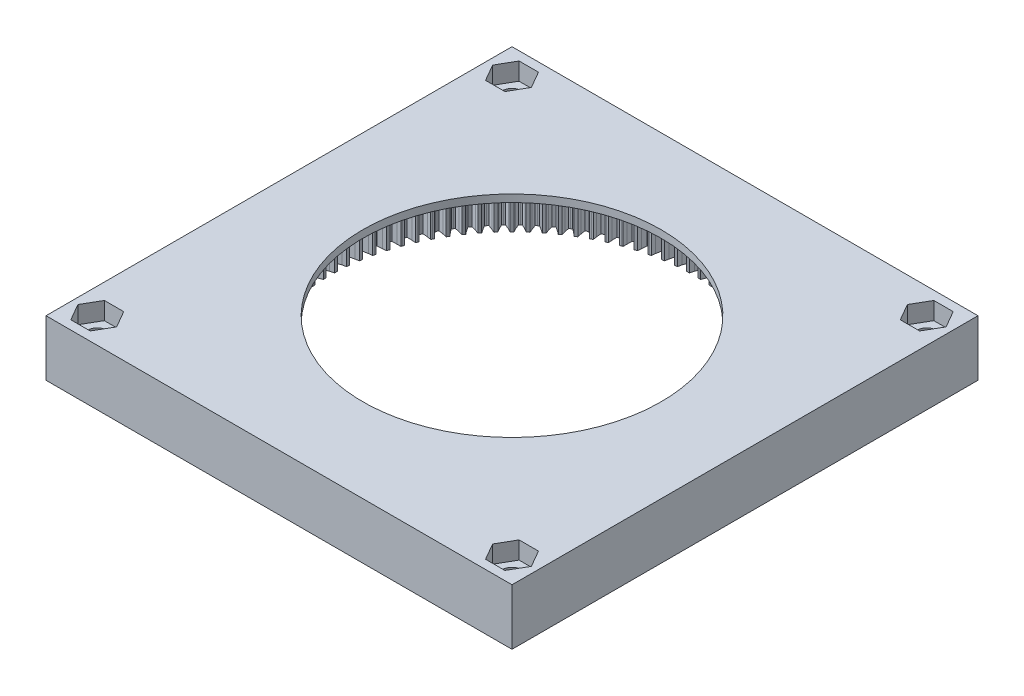
SolidWorks part; units mm, degrees
ref_plane "Front Plane" through (0, 0, 0) normal (0, 0, 1) x (1, 0, 0)
ref_plane "Top Plane" through (0, 0, 0) normal (0, 1, 0) x (1, 0, 0)
ref_plane "Right Plane" through (0, 0, 0) normal (1, 0, 0) x (0, 0, -1)
sketch "Sketch1" plane through (0, 0, 0) normal (0, 1, 0) x (1, 0, 0)
  line L1 (-79.375, -79.375) -> (79.375, -79.375)
  line L2 (-79.375, -79.375) -> (-79.375, 79.375)
  line L3 (-79.375, 79.375) -> (79.375, 79.375)
  line L4 (79.375, -79.375) -> (79.375, 79.375)
  line L5 (-79.375, -79.375) -> (79.375, 79.375) construction
  line L6 (-79.375, 79.375) -> (79.375, -79.375) construction
  dimension "D2" = 158.75
extrude "Boss-Extrude1" add sketch "Sketch1" along normal blind 19.05
sketch "Sketch7" plane through (0, 0, 0) normal (0, 1, 0) x (1, 0, 0)
  line L1 (-70.6438, -70.6438) -> (70.6437, -70.6438) construction
  line L2 (-70.6438, -70.6438) -> (-70.6438, 70.6437) construction
  line L3 (-70.6438, 70.6437) -> (70.6437, 70.6437) construction
  line L4 (70.6437, -70.6438) -> (70.6437, 70.6437) construction
  line L5 (-70.6438, -70.6438) -> (70.6437, 70.6437) construction
  line L6 (-70.6438, 70.6437) -> (70.6437, -70.6438) construction
  circle A0 centre (-70.6438, 70.6437) radius 3.3731
  circle A1 centre (70.6437, 70.6437) radius 3.3731
  circle A2 centre (70.6437, -70.6438) radius 3.3731
  circle A3 centre (-70.6438, -70.6438) radius 3.3731
  point P0 (0, 0)
  dimension "D2" = 6.7462
  dimension "D1" = 141.2875
extrude "Cut-Extrude2" cut sketch "Sketch7" along normal up to surface (19.05 mm away) up to face at (0, 19.05, 0)
sketch "Sketch8" plane through (0, 0, 0) normal (0, 1, 0) x (1, 0, 0)
  circle A0 centre (0, 0) radius 50.8
  dimension "D1" = 101.6
extrude "Cut-Extrude3" cut sketch "Sketch8" along normal up to surface (19.05 mm away) up to face at (-70.6438, 19.05, 67.2706)
sketch "Sketch10" plane through (0, 0, 0) normal (0, -1, 0) x (1, 0, 0)
  line L0 (61.8949, -1.477) -> (63.199, -1.0966)
  line L1 (63.199, -1.0966) -> (64.768, -0.5126)
  line L2 (64.768, -0.5126) -> (64.77, 0)
  line L3 (64.77, 0) -> (64.768, 0.5126)
  line L4 (64.768, 0.5126) -> (63.199, 1.0966)
  line L5 (63.199, 1.0966) -> (61.8949, 1.477)
  line L6 (61.8949, 1.477) -> (61.8819, 1.9447)
  line L7 (61.8819, 1.9447) -> (61.8655, 2.4123)
  line L8 (61.8655, 2.4123) -> (63.1432, 2.8739)
  line L9 (63.1432, 2.8739) -> (64.6724, 3.5553)
  line L10 (64.6724, 3.5553) -> (64.6422, 4.0669)
  line L11 (64.6422, 4.0669) -> (64.608, 4.5784)
  line L12 (64.608, 4.5784) -> (63.0054, 5.0627)
  line L13 (63.0054, 5.0627) -> (61.68, 5.3605)
  line L14 (61.68, 5.3605) -> (61.6377, 5.8265)
  line L15 (61.6377, 5.8265) -> (61.5919, 6.2921)
  line L16 (61.5919, 6.2921) -> (62.8381, 6.833)
  line L17 (62.8381, 6.833) -> (64.3215, 7.6091)
  line L18 (64.3215, 7.6091) -> (64.2593, 8.1178)
  line L19 (64.2593, 8.1178) -> (64.193, 8.6261)
  line L20 (64.193, 8.6261) -> (62.5632, 9.0089)
  line L21 (62.5632, 9.0089) -> (61.2217, 9.2229)
  line L22 (61.2217, 9.2229) -> (61.1503, 9.6852)
  line L23 (61.1503, 9.6852) -> (61.0753, 10.1471)
  line L24 (61.0753, 10.1471) -> (62.2851, 10.7652)
  line L25 (62.2851, 10.7652) -> (63.7168, 11.6328)
  line L26 (63.7168, 11.6328) -> (63.6227, 12.1367)
  line L27 (63.6227, 12.1367) -> (63.5247, 12.6398)
  line L28 (63.5247, 12.6398) -> (61.8741, 12.9195)
  line L29 (61.8741, 12.9195) -> (60.5218, 13.0488)
  line L30 (60.5218, 13.0488) -> (60.4214, 13.5058)
  line L31 (60.4214, 13.5058) -> (60.3177, 13.962)
  line L32 (60.3177, 13.962) -> (61.4862, 14.6548)
  line L33 (61.4862, 14.6548) -> (62.8606, 15.6107)
  line L34 (62.8606, 15.6107) -> (62.7351, 16.1076)
  line L35 (62.7351, 16.1076) -> (62.6057, 16.6036)
  line L36 (62.6057, 16.6036) -> (60.9408, 16.7791)
  line L37 (60.9408, 16.7791) -> (59.583, 16.8233)
  line L38 (59.583, 16.8233) -> (59.4542, 17.273)
  line L39 (59.4542, 17.273) -> (59.322, 17.7218)
  line L40 (59.322, 17.7218) -> (60.4447, 18.4867)
  line L41 (60.4447, 18.4867) -> (61.7564, 19.5269)
  line L42 (61.7564, 19.5269) -> (61.5999, 20.015)
  line L43 (61.5999, 20.015) -> (61.4396, 20.5019)
  line L44 (61.4396, 20.5019) -> (59.767, 20.5725)
  line L45 (59.767, 20.5725) -> (58.4091, 20.5313)
  line L46 (58.4091, 20.5313) -> (58.2523, 20.9721)
  line L47 (58.2523, 20.9721) -> (58.0921, 21.4117)
  line L48 (58.0921, 21.4117) -> (59.1646, 22.2455)
  line L49 (59.1646, 22.2455) -> (60.4084, 23.3661)
  line L50 (60.4084, 23.3661) -> (60.2216, 23.8434)
  line L51 (60.2216, 23.8434) -> (60.031, 24.3193)
  line L52 (60.031, 24.3193) -> (58.3573, 24.2847)
  line L53 (58.3573, 24.2847) -> (57.0047, 24.1583)
  line L54 (57.0047, 24.1583) -> (56.8205, 24.5884)
  line L55 (56.8205, 24.5884) -> (56.633, 25.0171)
  line L56 (56.633, 25.0171) -> (57.6511, 25.9166)
  line L57 (57.6511, 25.9166) -> (58.8221, 27.1131)
  line L58 (58.8221, 27.1131) -> (58.6056, 27.5777)
  line L59 (58.6056, 27.5777) -> (58.3856, 28.0406)
  line L60 (58.3856, 28.0406) -> (56.7173, 27.901)
  line L61 (56.7173, 27.901) -> (55.3753, 27.69)
  line L62 (55.3753, 27.69) -> (55.1644, 28.1077)
  line L63 (55.1644, 28.1077) -> (54.9505, 28.5238)
  line L64 (54.9505, 28.5238) -> (55.91, 29.4854)
  line L65 (55.91, 29.4854) -> (57.0035, 30.753)
  line L66 (57.0035, 30.753) -> (56.7584, 31.2032)
  line L67 (56.7584, 31.2032) -> (56.5097, 31.6514)
  line L68 (56.5097, 31.6514) -> (54.8534, 31.4073)
  line L69 (54.8534, 31.4073) -> (53.5273, 31.1124)
  line L70 (53.5273, 31.1124) -> (53.2907, 31.516)
  line L71 (53.2907, 31.516) -> (53.051, 31.9178)
  line L72 (53.051, 31.9178) -> (53.9483, 32.9379)
  line L73 (53.9483, 32.9379) -> (54.9601, 34.2716)
  line L74 (54.9601, 34.2716) -> (54.6871, 34.7055)
  line L75 (54.6871, 34.7055) -> (54.4108, 35.1372)
  line L76 (54.4108, 35.1372) -> (52.7731, 34.7896)
  line L77 (52.7731, 34.7896) -> (51.4681, 34.412)
  line L78 (51.4681, 34.412) -> (51.2066, 34.8)
  line L79 (51.2066, 34.8) -> (50.9422, 35.186)
  line L80 (50.9422, 35.186) -> (51.7736, 36.2603)
  line L81 (51.7736, 36.2603) -> (52.6997, 37.655)
  line L82 (52.6997, 37.655) -> (52.4, 38.0709)
  line L83 (52.4, 38.0709) -> (52.0971, 38.4843)
  line L84 (52.0971, 38.4843) -> (50.4845, 38.0346)
  line L85 (50.4845, 38.0346) -> (49.2058, 37.5758)
  line L86 (49.2058, 37.5758) -> (48.9205, 37.9466)
  line L87 (48.9205, 37.9466) -> (48.6323, 38.3152)
  line L88 (48.6323, 38.3152) -> (49.3946, 39.4396)
  line L89 (49.3946, 39.4396) -> (50.2313, 40.8897)
  line L90 (50.2313, 40.8897) -> (49.9061, 41.286)
  line L91 (49.9061, 41.286) -> (49.5779, 41.6796)
  line L92 (49.5779, 41.6796) -> (47.9967, 41.1295)
  line L93 (47.9967, 41.1295) -> (46.7493, 40.5913)
  line L94 (46.7493, 40.5913) -> (46.4413, 40.9435)
  line L95 (46.4413, 40.9435) -> (46.1305, 41.2933)
  line L96 (46.1305, 41.2933) -> (46.8207, 42.4633)
  line L97 (46.8207, 42.4633) -> (47.5647, 43.9631)
  line L98 (47.5647, 43.9631) -> (47.2153, 44.3381)
  line L99 (47.2153, 44.3381) -> (46.8629, 44.7104)
  line L100 (46.8629, 44.7104) -> (45.3194, 44.0621)
  line L101 (45.3194, 44.0621) -> (44.1083, 43.4467)
  line L102 (44.1083, 43.4467) -> (43.7787, 43.7787)
  line L103 (43.7787, 43.7787) -> (43.4467, 44.1083)
  line L104 (43.4467, 44.1083) -> (44.0621, 45.3194)
  line L105 (44.0621, 45.3194) -> (44.7104, 46.8629)
  line L106 (44.7104, 46.8629) -> (44.3381, 47.2153)
  line L107 (44.3381, 47.2153) -> (43.9631, 47.5647)
  line L108 (43.9631, 47.5647) -> (42.4633, 46.8207)
  line L109 (42.4633, 46.8207) -> (41.2933, 46.1305)
  line L110 (41.2933, 46.1305) -> (40.9435, 46.4413)
  line L111 (40.9435, 46.4413) -> (40.5913, 46.7493)
  line L112 (40.5913, 46.7493) -> (41.1295, 47.9967)
  line L113 (41.1295, 47.9967) -> (41.6796, 49.5779)
  line L114 (41.6796, 49.5779) -> (41.286, 49.9061)
  line L115 (41.286, 49.9061) -> (40.8897, 50.2313)
  line L116 (40.8897, 50.2313) -> (39.4396, 49.3946)
  line L117 (39.4396, 49.3946) -> (38.3152, 48.6323)
  line L118 (38.3152, 48.6323) -> (37.9466, 48.9205)
  line L119 (37.9466, 48.9205) -> (37.5758, 49.2058)
  line L120 (37.5758, 49.2058) -> (38.0346, 50.4845)
  line L121 (38.0346, 50.4845) -> (38.4843, 52.0971)
  line L122 (38.4843, 52.0971) -> (38.0709, 52.4)
  line L123 (38.0709, 52.4) -> (37.655, 52.6997)
  line L124 (37.655, 52.6997) -> (36.2603, 51.7736)
  line L125 (36.2603, 51.7736) -> (35.186, 50.9422)
  line L126 (35.186, 50.9422) -> (34.8, 51.2066)
  line L127 (34.8, 51.2066) -> (34.412, 51.4681)
  line L128 (34.412, 51.4681) -> (34.7896, 52.7731)
  line L129 (34.7896, 52.7731) -> (35.1372, 54.4108)
  line L130 (35.1372, 54.4108) -> (34.7055, 54.6871)
  line L131 (34.7055, 54.6871) -> (34.2716, 54.9601)
  line L132 (34.2716, 54.9601) -> (32.9379, 53.9483)
  line L133 (32.9379, 53.9483) -> (31.9178, 53.051)
  line L134 (31.9178, 53.051) -> (31.516, 53.2907)
  line L135 (31.516, 53.2907) -> (31.1124, 53.5273)
  line L136 (31.1124, 53.5273) -> (31.4073, 54.8534)
  line L137 (31.4073, 54.8534) -> (31.6514, 56.5097)
  line L138 (31.6514, 56.5097) -> (31.2032, 56.7584)
  line L139 (31.2032, 56.7584) -> (30.753, 57.0035)
  line L140 (30.753, 57.0035) -> (29.4854, 55.91)
  line L141 (29.4854, 55.91) -> (28.5238, 54.9505)
  line L142 (28.5238, 54.9505) -> (28.1077, 55.1644)
  line L143 (28.1077, 55.1644) -> (27.69, 55.3753)
  line L144 (27.69, 55.3753) -> (27.901, 56.7173)
  line L145 (27.901, 56.7173) -> (28.0406, 58.3856)
  line L146 (28.0406, 58.3856) -> (27.5777, 58.6056)
  line L147 (27.5777, 58.6056) -> (27.1131, 58.8221)
  line L148 (27.1131, 58.8221) -> (25.9166, 57.6511)
  line L149 (25.9166, 57.6511) -> (25.0171, 56.633)
  line L150 (25.0171, 56.633) -> (24.5884, 56.8205)
  line L151 (24.5884, 56.8205) -> (24.1583, 57.0047)
  line L152 (24.1583, 57.0047) -> (24.2847, 58.3573)
  line L153 (24.2847, 58.3573) -> (24.3193, 60.031)
  line L154 (24.3193, 60.031) -> (23.8434, 60.2216)
  line L155 (23.8434, 60.2216) -> (23.3661, 60.4084)
  line L156 (23.3661, 60.4084) -> (22.2455, 59.1646)
  line L157 (22.2455, 59.1646) -> (21.4117, 58.0921)
  line L158 (21.4117, 58.0921) -> (20.9721, 58.2523)
  line L159 (20.9721, 58.2523) -> (20.5313, 58.4091)
  line L160 (20.5313, 58.4091) -> (20.5725, 59.767)
  line L161 (20.5725, 59.767) -> (20.5019, 61.4396)
  line L162 (20.5019, 61.4396) -> (20.015, 61.5999)
  line L163 (20.015, 61.5999) -> (19.5269, 61.7564)
  line L164 (19.5269, 61.7564) -> (18.4867, 60.4447)
  line L165 (18.4867, 60.4447) -> (17.7218, 59.322)
  line L166 (17.7218, 59.322) -> (17.273, 59.4542)
  line L167 (17.273, 59.4542) -> (16.8233, 59.583)
  line L168 (16.8233, 59.583) -> (16.7791, 60.9408)
  line L169 (16.7791, 60.9408) -> (16.6036, 62.6057)
  line L170 (16.6036, 62.6057) -> (16.1076, 62.7351)
  line L171 (16.1076, 62.7351) -> (15.6107, 62.8606)
  line L172 (15.6107, 62.8606) -> (14.6548, 61.4862)
  line L173 (14.6548, 61.4862) -> (13.962, 60.3177)
  line L174 (13.962, 60.3177) -> (13.5058, 60.4214)
  line L175 (13.5058, 60.4214) -> (13.0488, 60.5218)
  line L176 (13.0488, 60.5218) -> (12.9195, 61.8741)
  line L177 (12.9195, 61.8741) -> (12.6398, 63.5247)
  line L178 (12.6398, 63.5247) -> (12.1367, 63.6227)
  line L179 (12.1367, 63.6227) -> (11.6328, 63.7168)
  line L180 (11.6328, 63.7168) -> (10.7652, 62.2851)
  line L181 (10.7652, 62.2851) -> (10.1471, 61.0753)
  line L182 (10.1471, 61.0753) -> (9.6852, 61.1503)
  line L183 (9.6852, 61.1503) -> (9.2229, 61.2217)
  line L184 (9.2229, 61.2217) -> (9.0089, 62.5632)
  line L185 (9.0089, 62.5632) -> (8.6261, 64.193)
  line L186 (8.6261, 64.193) -> (8.1178, 64.2593)
  line L187 (8.1178, 64.2593) -> (7.6091, 64.3215)
  line L188 (7.6091, 64.3215) -> (6.833, 62.8381)
  line L189 (6.833, 62.8381) -> (6.2921, 61.5919)
  line L190 (6.2921, 61.5919) -> (5.8265, 61.6377)
  line L191 (5.8265, 61.6377) -> (5.3605, 61.68)
  line L192 (5.3605, 61.68) -> (5.0627, 63.0054)
  line L193 (5.0627, 63.0054) -> (4.5784, 64.608)
  line L194 (4.5784, 64.608) -> (4.0669, 64.6422)
  line L195 (4.0669, 64.6422) -> (3.5553, 64.6724)
  line L196 (3.5553, 64.6724) -> (2.8739, 63.1432)
  line L197 (2.8739, 63.1432) -> (2.4123, 61.8655)
  line L198 (2.4123, 61.8655) -> (1.9447, 61.8819)
  line L199 (1.9447, 61.8819) -> (1.477, 61.8949)
  line L200 (1.477, 61.8949) -> (1.0966, 63.199)
  line L201 (1.0966, 63.199) -> (0.5126, 64.768)
  line L202 (0.5126, 64.768) -> (0, 64.77)
  line L203 (0, 64.77) -> (-0.5126, 64.768)
  line L204 (-0.5126, 64.768) -> (-1.0966, 63.199)
  line L205 (-1.0966, 63.199) -> (-1.477, 61.8949)
  line L206 (-1.477, 61.8949) -> (-1.9447, 61.8819)
  line L207 (-1.9447, 61.8819) -> (-2.4123, 61.8655)
  line L208 (-2.4123, 61.8655) -> (-2.8739, 63.1432)
  line L209 (-2.8739, 63.1432) -> (-3.5553, 64.6724)
  line L210 (-3.5553, 64.6724) -> (-4.0669, 64.6422)
  line L211 (-4.0669, 64.6422) -> (-4.5784, 64.608)
  line L212 (-4.5784, 64.608) -> (-5.0627, 63.0054)
  line L213 (-5.0627, 63.0054) -> (-5.3605, 61.68)
  line L214 (-5.3605, 61.68) -> (-5.8265, 61.6377)
  line L215 (-5.8265, 61.6377) -> (-6.2921, 61.5919)
  line L216 (-6.2921, 61.5919) -> (-6.833, 62.8381)
  line L217 (-6.833, 62.8381) -> (-7.6091, 64.3215)
  line L218 (-7.6091, 64.3215) -> (-8.1178, 64.2593)
  line L219 (-8.1178, 64.2593) -> (-8.6261, 64.193)
  line L220 (-8.6261, 64.193) -> (-9.0089, 62.5632)
  line L221 (-9.0089, 62.5632) -> (-9.2229, 61.2217)
  line L222 (-9.2229, 61.2217) -> (-9.6852, 61.1503)
  line L223 (-9.6852, 61.1503) -> (-10.1471, 61.0753)
  line L224 (-10.1471, 61.0753) -> (-10.7652, 62.2851)
  line L225 (-10.7652, 62.2851) -> (-11.6328, 63.7168)
  line L226 (-11.6328, 63.7168) -> (-12.1367, 63.6227)
  line L227 (-12.1367, 63.6227) -> (-12.6398, 63.5247)
  line L228 (-12.6398, 63.5247) -> (-12.9195, 61.8741)
  line L229 (-12.9195, 61.8741) -> (-13.0488, 60.5218)
  line L230 (-13.0488, 60.5218) -> (-13.5058, 60.4214)
  line L231 (-13.5058, 60.4214) -> (-13.962, 60.3177)
  line L232 (-13.962, 60.3177) -> (-14.6548, 61.4862)
  line L233 (-14.6548, 61.4862) -> (-15.6107, 62.8606)
  line L234 (-15.6107, 62.8606) -> (-16.1076, 62.7351)
  line L235 (-16.1076, 62.7351) -> (-16.6036, 62.6057)
  line L236 (-16.6036, 62.6057) -> (-16.7791, 60.9408)
  line L237 (-16.7791, 60.9408) -> (-16.8233, 59.583)
  line L238 (-16.8233, 59.583) -> (-17.273, 59.4542)
  line L239 (-17.273, 59.4542) -> (-17.7218, 59.322)
  line L240 (-17.7218, 59.322) -> (-18.4867, 60.4447)
  line L241 (-18.4867, 60.4447) -> (-19.5269, 61.7564)
  line L242 (-19.5269, 61.7564) -> (-20.015, 61.5999)
  line L243 (-20.015, 61.5999) -> (-20.5019, 61.4396)
  line L244 (-20.5019, 61.4396) -> (-20.5725, 59.767)
  line L245 (-20.5725, 59.767) -> (-20.5313, 58.4091)
  line L246 (-20.5313, 58.4091) -> (-20.9721, 58.2523)
  line L247 (-20.9721, 58.2523) -> (-21.4117, 58.0921)
  line L248 (-21.4117, 58.0921) -> (-22.2455, 59.1646)
  line L249 (-22.2455, 59.1646) -> (-23.3661, 60.4084)
  line L250 (-23.3661, 60.4084) -> (-23.8434, 60.2216)
  line L251 (-23.8434, 60.2216) -> (-24.3193, 60.031)
  line L252 (-24.3193, 60.031) -> (-24.2847, 58.3573)
  line L253 (-24.2847, 58.3573) -> (-24.1583, 57.0047)
  line L254 (-24.1583, 57.0047) -> (-24.5884, 56.8205)
  line L255 (-24.5884, 56.8205) -> (-25.0171, 56.633)
  line L256 (-25.0171, 56.633) -> (-25.9166, 57.6511)
  line L257 (-25.9166, 57.6511) -> (-27.1131, 58.8221)
  line L258 (-27.1131, 58.8221) -> (-27.5777, 58.6056)
  line L259 (-27.5777, 58.6056) -> (-28.0406, 58.3856)
  line L260 (-28.0406, 58.3856) -> (-27.901, 56.7173)
  line L261 (-27.901, 56.7173) -> (-27.69, 55.3753)
  line L262 (-27.69, 55.3753) -> (-28.1077, 55.1644)
  line L263 (-28.1077, 55.1644) -> (-28.5238, 54.9505)
  line L264 (-28.5238, 54.9505) -> (-29.4854, 55.91)
  line L265 (-29.4854, 55.91) -> (-30.753, 57.0035)
  line L266 (-30.753, 57.0035) -> (-31.2032, 56.7584)
  line L267 (-31.2032, 56.7584) -> (-31.6514, 56.5097)
  line L268 (-31.6514, 56.5097) -> (-31.4073, 54.8534)
  line L269 (-31.4073, 54.8534) -> (-31.1124, 53.5273)
  line L270 (-31.1124, 53.5273) -> (-31.516, 53.2907)
  line L271 (-31.516, 53.2907) -> (-31.9178, 53.051)
  line L272 (-31.9178, 53.051) -> (-32.9379, 53.9483)
  line L273 (-32.9379, 53.9483) -> (-34.2716, 54.9601)
  line L274 (-34.2716, 54.9601) -> (-34.7055, 54.6871)
  line L275 (-34.7055, 54.6871) -> (-35.1372, 54.4108)
  line L276 (-35.1372, 54.4108) -> (-34.7896, 52.7731)
  line L277 (-34.7896, 52.7731) -> (-34.412, 51.4681)
  line L278 (-34.412, 51.4681) -> (-34.8, 51.2066)
  line L279 (-34.8, 51.2066) -> (-35.186, 50.9422)
  line L280 (-35.186, 50.9422) -> (-36.2603, 51.7736)
  line L281 (-36.2603, 51.7736) -> (-37.655, 52.6997)
  line L282 (-37.655, 52.6997) -> (-38.0709, 52.4)
  line L283 (-38.0709, 52.4) -> (-38.4843, 52.0971)
  line L284 (-38.4843, 52.0971) -> (-38.0346, 50.4845)
  line L285 (-38.0346, 50.4845) -> (-37.5758, 49.2058)
  line L286 (-37.5758, 49.2058) -> (-37.9466, 48.9205)
  line L287 (-37.9466, 48.9205) -> (-38.3152, 48.6323)
  line L288 (-38.3152, 48.6323) -> (-39.4396, 49.3946)
  line L289 (-39.4396, 49.3946) -> (-40.8897, 50.2313)
  line L290 (-40.8897, 50.2313) -> (-41.286, 49.9061)
  line L291 (-41.286, 49.9061) -> (-41.6796, 49.5779)
  line L292 (-41.6796, 49.5779) -> (-41.1295, 47.9967)
  line L293 (-41.1295, 47.9967) -> (-40.5913, 46.7493)
  line L294 (-40.5913, 46.7493) -> (-40.9435, 46.4413)
  line L295 (-40.9435, 46.4413) -> (-41.2933, 46.1305)
  line L296 (-41.2933, 46.1305) -> (-42.4633, 46.8207)
  line L297 (-42.4633, 46.8207) -> (-43.9631, 47.5647)
  line L298 (-43.9631, 47.5647) -> (-44.3381, 47.2153)
  line L299 (-44.3381, 47.2153) -> (-44.7104, 46.8629)
  line L300 (-44.7104, 46.8629) -> (-44.0621, 45.3194)
  line L301 (-44.0621, 45.3194) -> (-43.4467, 44.1083)
  line L302 (-43.4467, 44.1083) -> (-43.7787, 43.7787)
  line L303 (-43.7787, 43.7787) -> (-44.1083, 43.4467)
  line L304 (-44.1083, 43.4467) -> (-45.3194, 44.0621)
  line L305 (-45.3194, 44.0621) -> (-46.8629, 44.7104)
  line L306 (-46.8629, 44.7104) -> (-47.2153, 44.3381)
  line L307 (-47.2153, 44.3381) -> (-47.5647, 43.9631)
  line L308 (-47.5647, 43.9631) -> (-46.8207, 42.4633)
  line L309 (-46.8207, 42.4633) -> (-46.1305, 41.2933)
  line L310 (-46.1305, 41.2933) -> (-46.4413, 40.9435)
  line L311 (-46.4413, 40.9435) -> (-46.7493, 40.5913)
  line L312 (-46.7493, 40.5913) -> (-47.9967, 41.1295)
  line L313 (-47.9967, 41.1295) -> (-49.5779, 41.6796)
  line L314 (-49.5779, 41.6796) -> (-49.9061, 41.286)
  line L315 (-49.9061, 41.286) -> (-50.2313, 40.8897)
  line L316 (-50.2313, 40.8897) -> (-49.3946, 39.4396)
  line L317 (-49.3946, 39.4396) -> (-48.6323, 38.3152)
  line L318 (-48.6323, 38.3152) -> (-48.9205, 37.9466)
  line L319 (-48.9205, 37.9466) -> (-49.2058, 37.5758)
  line L320 (-49.2058, 37.5758) -> (-50.4845, 38.0346)
  line L321 (-50.4845, 38.0346) -> (-52.0971, 38.4843)
  line L322 (-52.0971, 38.4843) -> (-52.4, 38.0709)
  line L323 (-52.4, 38.0709) -> (-52.6997, 37.655)
  line L324 (-52.6997, 37.655) -> (-51.7736, 36.2603)
  line L325 (-51.7736, 36.2603) -> (-50.9422, 35.186)
  line L326 (-50.9422, 35.186) -> (-51.2066, 34.8)
  line L327 (-51.2066, 34.8) -> (-51.4681, 34.412)
  line L328 (-51.4681, 34.412) -> (-52.7731, 34.7896)
  line L329 (-52.7731, 34.7896) -> (-54.4108, 35.1372)
  line L330 (-54.4108, 35.1372) -> (-54.6871, 34.7055)
  line L331 (-54.6871, 34.7055) -> (-54.9601, 34.2716)
  line L332 (-54.9601, 34.2716) -> (-53.9483, 32.9379)
  line L333 (-53.9483, 32.9379) -> (-53.051, 31.9178)
  line L334 (-53.051, 31.9178) -> (-53.2907, 31.516)
  line L335 (-53.2907, 31.516) -> (-53.5273, 31.1124)
  line L336 (-53.5273, 31.1124) -> (-54.8534, 31.4073)
  line L337 (-54.8534, 31.4073) -> (-56.5097, 31.6514)
  line L338 (-56.5097, 31.6514) -> (-56.7584, 31.2032)
  line L339 (-56.7584, 31.2032) -> (-57.0035, 30.753)
  line L340 (-57.0035, 30.753) -> (-55.91, 29.4854)
  line L341 (-55.91, 29.4854) -> (-54.9505, 28.5238)
  line L342 (-54.9505, 28.5238) -> (-55.1644, 28.1077)
  line L343 (-55.1644, 28.1077) -> (-55.3753, 27.69)
  line L344 (-55.3753, 27.69) -> (-56.7173, 27.901)
  line L345 (-56.7173, 27.901) -> (-58.3856, 28.0406)
  line L346 (-58.3856, 28.0406) -> (-58.6056, 27.5777)
  line L347 (-58.6056, 27.5777) -> (-58.8221, 27.1131)
  line L348 (-58.8221, 27.1131) -> (-57.6511, 25.9166)
  line L349 (-57.6511, 25.9166) -> (-56.633, 25.0171)
  line L350 (-56.633, 25.0171) -> (-56.8205, 24.5884)
  line L351 (-56.8205, 24.5884) -> (-57.0047, 24.1583)
  line L352 (-57.0047, 24.1583) -> (-58.3573, 24.2847)
  line L353 (-58.3573, 24.2847) -> (-60.031, 24.3193)
  line L354 (-60.031, 24.3193) -> (-60.2216, 23.8434)
  line L355 (-60.2216, 23.8434) -> (-60.4084, 23.3661)
  line L356 (-60.4084, 23.3661) -> (-59.1646, 22.2455)
  line L357 (-59.1646, 22.2455) -> (-58.0921, 21.4117)
  line L358 (-58.0921, 21.4117) -> (-58.2523, 20.9721)
  line L359 (-58.2523, 20.9721) -> (-58.4091, 20.5313)
  line L360 (-58.4091, 20.5313) -> (-59.767, 20.5725)
  line L361 (-59.767, 20.5725) -> (-61.4396, 20.5019)
  line L362 (-61.4396, 20.5019) -> (-61.5999, 20.015)
  line L363 (-61.5999, 20.015) -> (-61.7564, 19.5269)
  line L364 (-61.7564, 19.5269) -> (-60.4447, 18.4867)
  line L365 (-60.4447, 18.4867) -> (-59.322, 17.7218)
  line L366 (-59.322, 17.7218) -> (-59.4542, 17.273)
  line L367 (-59.4542, 17.273) -> (-59.583, 16.8233)
  line L368 (-59.583, 16.8233) -> (-60.9408, 16.7791)
  line L369 (-60.9408, 16.7791) -> (-62.6057, 16.6036)
  line L370 (-62.6057, 16.6036) -> (-62.7351, 16.1076)
  line L371 (-62.7351, 16.1076) -> (-62.8606, 15.6107)
  line L372 (-62.8606, 15.6107) -> (-61.4862, 14.6548)
  line L373 (-61.4862, 14.6548) -> (-60.3177, 13.962)
  line L374 (-60.3177, 13.962) -> (-60.4214, 13.5058)
  line L375 (-60.4214, 13.5058) -> (-60.5218, 13.0488)
  line L376 (-60.5218, 13.0488) -> (-61.8741, 12.9195)
  line L377 (-61.8741, 12.9195) -> (-63.5247, 12.6398)
  line L378 (-63.5247, 12.6398) -> (-63.6227, 12.1367)
  line L379 (-63.6227, 12.1367) -> (-63.7168, 11.6328)
  line L380 (-63.7168, 11.6328) -> (-62.2851, 10.7652)
  line L381 (-62.2851, 10.7652) -> (-61.0753, 10.1471)
  line L382 (-61.0753, 10.1471) -> (-61.1503, 9.6852)
  line L383 (-61.1503, 9.6852) -> (-61.2217, 9.2229)
  line L384 (-61.2217, 9.2229) -> (-62.5632, 9.0089)
  line L385 (-62.5632, 9.0089) -> (-64.193, 8.6261)
  line L386 (-64.193, 8.6261) -> (-64.2593, 8.1178)
  line L387 (-64.2593, 8.1178) -> (-64.3215, 7.6091)
  line L388 (-64.3215, 7.6091) -> (-62.8381, 6.833)
  line L389 (-62.8381, 6.833) -> (-61.5919, 6.2921)
  line L390 (-61.5919, 6.2921) -> (-61.6377, 5.8265)
  line L391 (-61.6377, 5.8265) -> (-61.68, 5.3605)
  line L392 (-61.68, 5.3605) -> (-63.0054, 5.0627)
  line L393 (-63.0054, 5.0627) -> (-64.608, 4.5784)
  line L394 (-64.608, 4.5784) -> (-64.6422, 4.0669)
  line L395 (-64.6422, 4.0669) -> (-64.6724, 3.5553)
  line L396 (-64.6724, 3.5553) -> (-63.1432, 2.8739)
  line L397 (-63.1432, 2.8739) -> (-61.8655, 2.4123)
  line L398 (-61.8655, 2.4123) -> (-61.8819, 1.9447)
  line L399 (-61.8819, 1.9447) -> (-61.8949, 1.477)
  line L400 (-61.8949, 1.477) -> (-63.199, 1.0966)
  line L401 (-63.199, 1.0966) -> (-64.768, 0.5126)
  line L402 (-64.768, 0.5126) -> (-64.77, 0)
  line L403 (-64.77, 0) -> (-64.768, -0.5126)
  line L404 (-64.768, -0.5126) -> (-63.199, -1.0966)
  line L405 (-63.199, -1.0966) -> (-61.8949, -1.477)
  line L406 (-61.8949, -1.477) -> (-61.8819, -1.9447)
  line L407 (-61.8819, -1.9447) -> (-61.8655, -2.4123)
  line L408 (-61.8655, -2.4123) -> (-63.1432, -2.8739)
  line L409 (-63.1432, -2.8739) -> (-64.6724, -3.5553)
  line L410 (-64.6724, -3.5553) -> (-64.6422, -4.0669)
  line L411 (-64.6422, -4.0669) -> (-64.608, -4.5784)
  line L412 (-64.608, -4.5784) -> (-63.0054, -5.0627)
  line L413 (-63.0054, -5.0627) -> (-61.68, -5.3605)
  line L414 (-61.68, -5.3605) -> (-61.6377, -5.8265)
  line L415 (-61.6377, -5.8265) -> (-61.5919, -6.2921)
  line L416 (-61.5919, -6.2921) -> (-62.8381, -6.833)
  line L417 (-62.8381, -6.833) -> (-64.3215, -7.6091)
  line L418 (-64.3215, -7.6091) -> (-64.2593, -8.1178)
  line L419 (-64.2593, -8.1178) -> (-64.193, -8.6261)
  line L420 (-64.193, -8.6261) -> (-62.5632, -9.0089)
  line L421 (-62.5632, -9.0089) -> (-61.2217, -9.2229)
  line L422 (-61.2217, -9.2229) -> (-61.1503, -9.6852)
  line L423 (-61.1503, -9.6852) -> (-61.0753, -10.1471)
  line L424 (-61.0753, -10.1471) -> (-62.2851, -10.7652)
  line L425 (-62.2851, -10.7652) -> (-63.7168, -11.6328)
  line L426 (-63.7168, -11.6328) -> (-63.6227, -12.1367)
  line L427 (-63.6227, -12.1367) -> (-63.5247, -12.6398)
  line L428 (-63.5247, -12.6398) -> (-61.8741, -12.9195)
  line L429 (-61.8741, -12.9195) -> (-60.5218, -13.0488)
  line L430 (-60.5218, -13.0488) -> (-60.4214, -13.5058)
  line L431 (-60.4214, -13.5058) -> (-60.3177, -13.962)
  line L432 (-60.3177, -13.962) -> (-61.4862, -14.6548)
  line L433 (-61.4862, -14.6548) -> (-62.8606, -15.6107)
  line L434 (-62.8606, -15.6107) -> (-62.7351, -16.1076)
  line L435 (-62.7351, -16.1076) -> (-62.6057, -16.6036)
  line L436 (-62.6057, -16.6036) -> (-60.9408, -16.7791)
  line L437 (-60.9408, -16.7791) -> (-59.583, -16.8233)
  line L438 (-59.583, -16.8233) -> (-59.4542, -17.273)
  line L439 (-59.4542, -17.273) -> (-59.322, -17.7218)
  line L440 (-59.322, -17.7218) -> (-60.4447, -18.4867)
  line L441 (-60.4447, -18.4867) -> (-61.7564, -19.5269)
  line L442 (-61.7564, -19.5269) -> (-61.5999, -20.015)
  line L443 (-61.5999, -20.015) -> (-61.4396, -20.5019)
  line L444 (-61.4396, -20.5019) -> (-59.767, -20.5725)
  line L445 (-59.767, -20.5725) -> (-58.4091, -20.5313)
  line L446 (-58.4091, -20.5313) -> (-58.2523, -20.9721)
  line L447 (-58.2523, -20.9721) -> (-58.0921, -21.4117)
  line L448 (-58.0921, -21.4117) -> (-59.1646, -22.2455)
  line L449 (-59.1646, -22.2455) -> (-60.4084, -23.3661)
  line L450 (-60.4084, -23.3661) -> (-60.2216, -23.8434)
  line L451 (-60.2216, -23.8434) -> (-60.031, -24.3193)
  line L452 (-60.031, -24.3193) -> (-58.3573, -24.2847)
  line L453 (-58.3573, -24.2847) -> (-57.0047, -24.1583)
  line L454 (-57.0047, -24.1583) -> (-56.8205, -24.5884)
  line L455 (-56.8205, -24.5884) -> (-56.633, -25.0171)
  line L456 (-56.633, -25.0171) -> (-57.6511, -25.9166)
  line L457 (-57.6511, -25.9166) -> (-58.8221, -27.1131)
  line L458 (-58.8221, -27.1131) -> (-58.6056, -27.5777)
  line L459 (-58.6056, -27.5777) -> (-58.3856, -28.0406)
  line L460 (-58.3856, -28.0406) -> (-56.7173, -27.901)
  line L461 (-56.7173, -27.901) -> (-55.3753, -27.69)
  line L462 (-55.3753, -27.69) -> (-55.1644, -28.1077)
  line L463 (-55.1644, -28.1077) -> (-54.9505, -28.5238)
  line L464 (-54.9505, -28.5238) -> (-55.91, -29.4854)
  line L465 (-55.91, -29.4854) -> (-57.0035, -30.753)
  line L466 (-57.0035, -30.753) -> (-56.7584, -31.2032)
  line L467 (-56.7584, -31.2032) -> (-56.5097, -31.6514)
  line L468 (-56.5097, -31.6514) -> (-54.8534, -31.4073)
  line L469 (-54.8534, -31.4073) -> (-53.5273, -31.1124)
  line L470 (-53.5273, -31.1124) -> (-53.2907, -31.516)
  line L471 (-53.2907, -31.516) -> (-53.051, -31.9178)
  line L472 (-53.051, -31.9178) -> (-53.9483, -32.9379)
  line L473 (-53.9483, -32.9379) -> (-54.9601, -34.2716)
  line L474 (-54.9601, -34.2716) -> (-54.6871, -34.7055)
  line L475 (-54.6871, -34.7055) -> (-54.4108, -35.1372)
  line L476 (-54.4108, -35.1372) -> (-52.7731, -34.7896)
  line L477 (-52.7731, -34.7896) -> (-51.4681, -34.412)
  line L478 (-51.4681, -34.412) -> (-51.2066, -34.8)
  line L479 (-51.2066, -34.8) -> (-50.9422, -35.186)
  line L480 (-50.9422, -35.186) -> (-51.7736, -36.2603)
  line L481 (-51.7736, -36.2603) -> (-52.6997, -37.655)
  line L482 (-52.6997, -37.655) -> (-52.4, -38.0709)
  line L483 (-52.4, -38.0709) -> (-52.0971, -38.4843)
  line L484 (-52.0971, -38.4843) -> (-50.4845, -38.0346)
  line L485 (-50.4845, -38.0346) -> (-49.2058, -37.5758)
  line L486 (-49.2058, -37.5758) -> (-48.9205, -37.9466)
  line L487 (-48.9205, -37.9466) -> (-48.6323, -38.3152)
  line L488 (-48.6323, -38.3152) -> (-49.3946, -39.4396)
  line L489 (-49.3946, -39.4396) -> (-50.2313, -40.8897)
  line L490 (-50.2313, -40.8897) -> (-49.9061, -41.286)
  line L491 (-49.9061, -41.286) -> (-49.5779, -41.6796)
  line L492 (-49.5779, -41.6796) -> (-47.9967, -41.1295)
  line L493 (-47.9967, -41.1295) -> (-46.7493, -40.5913)
  line L494 (-46.7493, -40.5913) -> (-46.4413, -40.9435)
  line L495 (-46.4413, -40.9435) -> (-46.1305, -41.2933)
  line L496 (-46.1305, -41.2933) -> (-46.8207, -42.4633)
  line L497 (-46.8207, -42.4633) -> (-47.5647, -43.9631)
  line L498 (-47.5647, -43.9631) -> (-47.2153, -44.3381)
  line L499 (-47.2153, -44.3381) -> (-46.8629, -44.7104)
  line L500 (-46.8629, -44.7104) -> (-45.3194, -44.0621)
  line L501 (-45.3194, -44.0621) -> (-44.1083, -43.4467)
  line L502 (-44.1083, -43.4467) -> (-43.7787, -43.7787)
  line L503 (-43.7787, -43.7787) -> (-43.4467, -44.1083)
  line L504 (-43.4467, -44.1083) -> (-44.0621, -45.3194)
  line L505 (-44.0621, -45.3194) -> (-44.7104, -46.8629)
  line L506 (-44.7104, -46.8629) -> (-44.3381, -47.2153)
  line L507 (-44.3381, -47.2153) -> (-43.9631, -47.5647)
  line L508 (-43.9631, -47.5647) -> (-42.4633, -46.8207)
  line L509 (-42.4633, -46.8207) -> (-41.2933, -46.1305)
  line L510 (-41.2933, -46.1305) -> (-40.9435, -46.4413)
  line L511 (-40.9435, -46.4413) -> (-40.5913, -46.7493)
  line L512 (-40.5913, -46.7493) -> (-41.1295, -47.9967)
  line L513 (-41.1295, -47.9967) -> (-41.6796, -49.5779)
  line L514 (-41.6796, -49.5779) -> (-41.286, -49.9061)
  line L515 (-41.286, -49.9061) -> (-40.8897, -50.2313)
  line L516 (-40.8897, -50.2313) -> (-39.4396, -49.3946)
  line L517 (-39.4396, -49.3946) -> (-38.3152, -48.6323)
  line L518 (-38.3152, -48.6323) -> (-37.9466, -48.9205)
  line L519 (-37.9466, -48.9205) -> (-37.5758, -49.2058)
  line L520 (-37.5758, -49.2058) -> (-38.0346, -50.4845)
  line L521 (-38.0346, -50.4845) -> (-38.4843, -52.0971)
  line L522 (-38.4843, -52.0971) -> (-38.0709, -52.4)
  line L523 (-38.0709, -52.4) -> (-37.655, -52.6997)
  line L524 (-37.655, -52.6997) -> (-36.2603, -51.7736)
  line L525 (-36.2603, -51.7736) -> (-35.186, -50.9422)
  line L526 (-35.186, -50.9422) -> (-34.8, -51.2066)
  line L527 (-34.8, -51.2066) -> (-34.412, -51.4681)
  line L528 (-34.412, -51.4681) -> (-34.7896, -52.7731)
  line L529 (-34.7896, -52.7731) -> (-35.1372, -54.4108)
  line L530 (-35.1372, -54.4108) -> (-34.7055, -54.6871)
  line L531 (-34.7055, -54.6871) -> (-34.2716, -54.9601)
  line L532 (-34.2716, -54.9601) -> (-32.9379, -53.9483)
  line L533 (-32.9379, -53.9483) -> (-31.9178, -53.051)
  line L534 (-31.9178, -53.051) -> (-31.516, -53.2907)
  line L535 (-31.516, -53.2907) -> (-31.1124, -53.5273)
  line L536 (-31.1124, -53.5273) -> (-31.4073, -54.8534)
  line L537 (-31.4073, -54.8534) -> (-31.6514, -56.5097)
  line L538 (-31.6514, -56.5097) -> (-31.2032, -56.7584)
  line L539 (-31.2032, -56.7584) -> (-30.753, -57.0035)
  line L540 (-30.753, -57.0035) -> (-29.4854, -55.91)
  line L541 (-29.4854, -55.91) -> (-28.5238, -54.9505)
  line L542 (-28.5238, -54.9505) -> (-28.1077, -55.1644)
  line L543 (-28.1077, -55.1644) -> (-27.69, -55.3753)
  line L544 (-27.69, -55.3753) -> (-27.901, -56.7173)
  line L545 (-27.901, -56.7173) -> (-28.0406, -58.3856)
  line L546 (-28.0406, -58.3856) -> (-27.5777, -58.6056)
  line L547 (-27.5777, -58.6056) -> (-27.1131, -58.8221)
  line L548 (-27.1131, -58.8221) -> (-25.9166, -57.6511)
  line L549 (-25.9166, -57.6511) -> (-25.0171, -56.633)
  line L550 (-25.0171, -56.633) -> (-24.5884, -56.8205)
  line L551 (-24.5884, -56.8205) -> (-24.1583, -57.0047)
  line L552 (-24.1583, -57.0047) -> (-24.2847, -58.3573)
  line L553 (-24.2847, -58.3573) -> (-24.3193, -60.031)
  line L554 (-24.3193, -60.031) -> (-23.8434, -60.2216)
  line L555 (-23.8434, -60.2216) -> (-23.3661, -60.4084)
  line L556 (-23.3661, -60.4084) -> (-22.2455, -59.1646)
  line L557 (-22.2455, -59.1646) -> (-21.4117, -58.0921)
  line L558 (-21.4117, -58.0921) -> (-20.9721, -58.2523)
  line L559 (-20.9721, -58.2523) -> (-20.5313, -58.4091)
  line L560 (-20.5313, -58.4091) -> (-20.5725, -59.767)
  line L561 (-20.5725, -59.767) -> (-20.5019, -61.4396)
  line L562 (-20.5019, -61.4396) -> (-20.015, -61.5999)
  line L563 (-20.015, -61.5999) -> (-19.5269, -61.7564)
  line L564 (-19.5269, -61.7564) -> (-18.4867, -60.4447)
  line L565 (-18.4867, -60.4447) -> (-17.7218, -59.322)
  line L566 (-17.7218, -59.322) -> (-17.273, -59.4542)
  line L567 (-17.273, -59.4542) -> (-16.8233, -59.583)
  line L568 (-16.8233, -59.583) -> (-16.7791, -60.9408)
  line L569 (-16.7791, -60.9408) -> (-16.6036, -62.6057)
  line L570 (-16.6036, -62.6057) -> (-16.1076, -62.7351)
  line L571 (-16.1076, -62.7351) -> (-15.6107, -62.8606)
  line L572 (-15.6107, -62.8606) -> (-14.6548, -61.4862)
  line L573 (-14.6548, -61.4862) -> (-13.962, -60.3177)
  line L574 (-13.962, -60.3177) -> (-13.5058, -60.4214)
  line L575 (-13.5058, -60.4214) -> (-13.0488, -60.5218)
  line L576 (-13.0488, -60.5218) -> (-12.9195, -61.8741)
  line L577 (-12.9195, -61.8741) -> (-12.6398, -63.5247)
  line L578 (-12.6398, -63.5247) -> (-12.1367, -63.6227)
  line L579 (-12.1367, -63.6227) -> (-11.6328, -63.7168)
  line L580 (-11.6328, -63.7168) -> (-10.7652, -62.2851)
  line L581 (-10.7652, -62.2851) -> (-10.1471, -61.0753)
  line L582 (-10.1471, -61.0753) -> (-9.6852, -61.1503)
  line L583 (-9.6852, -61.1503) -> (-9.2229, -61.2217)
  line L584 (-9.2229, -61.2217) -> (-9.0089, -62.5632)
  line L585 (-9.0089, -62.5632) -> (-8.6261, -64.193)
  line L586 (-8.6261, -64.193) -> (-8.1178, -64.2593)
  line L587 (-8.1178, -64.2593) -> (-7.6091, -64.3215)
  line L588 (-7.6091, -64.3215) -> (-6.833, -62.8381)
  line L589 (-6.833, -62.8381) -> (-6.2921, -61.5919)
  line L590 (-6.2921, -61.5919) -> (-5.8265, -61.6377)
  line L591 (-5.8265, -61.6377) -> (-5.3605, -61.68)
  line L592 (-5.3605, -61.68) -> (-5.0627, -63.0054)
  line L593 (-5.0627, -63.0054) -> (-4.5784, -64.608)
  line L594 (-4.5784, -64.608) -> (-4.0669, -64.6422)
  line L595 (-4.0669, -64.6422) -> (-3.5553, -64.6724)
  line L596 (-3.5553, -64.6724) -> (-2.8739, -63.1432)
  line L597 (-2.8739, -63.1432) -> (-2.4123, -61.8655)
  line L598 (-2.4123, -61.8655) -> (-1.9447, -61.8819)
  line L599 (-1.9447, -61.8819) -> (-1.477, -61.8949)
  line L600 (-1.477, -61.8949) -> (-1.0966, -63.199)
  line L601 (-1.0966, -63.199) -> (-0.5126, -64.768)
  line L602 (-0.5126, -64.768) -> (0, -64.77)
  line L603 (0, -64.77) -> (0.5126, -64.768)
  line L604 (0.5126, -64.768) -> (1.0966, -63.199)
  line L605 (1.0966, -63.199) -> (1.477, -61.8949)
  line L606 (1.477, -61.8949) -> (1.9447, -61.8819)
  line L607 (1.9447, -61.8819) -> (2.4123, -61.8655)
  line L608 (2.4123, -61.8655) -> (2.8739, -63.1432)
  line L609 (2.8739, -63.1432) -> (3.5553, -64.6724)
  line L610 (3.5553, -64.6724) -> (4.0669, -64.6422)
  line L611 (4.0669, -64.6422) -> (4.5784, -64.608)
  line L612 (4.5784, -64.608) -> (5.0627, -63.0054)
  line L613 (5.0627, -63.0054) -> (5.3605, -61.68)
  line L614 (5.3605, -61.68) -> (5.8265, -61.6377)
  line L615 (5.8265, -61.6377) -> (6.2921, -61.5919)
  line L616 (6.2921, -61.5919) -> (6.833, -62.8381)
  line L617 (6.833, -62.8381) -> (7.6091, -64.3215)
  line L618 (7.6091, -64.3215) -> (8.1178, -64.2593)
  line L619 (8.1178, -64.2593) -> (8.6261, -64.193)
  line L620 (8.6261, -64.193) -> (9.0089, -62.5632)
  line L621 (9.0089, -62.5632) -> (9.2229, -61.2217)
  line L622 (9.2229, -61.2217) -> (9.6852, -61.1503)
  line L623 (9.6852, -61.1503) -> (10.1471, -61.0753)
  line L624 (10.1471, -61.0753) -> (10.7652, -62.2851)
  line L625 (10.7652, -62.2851) -> (11.6328, -63.7168)
  line L626 (11.6328, -63.7168) -> (12.1367, -63.6227)
  line L627 (12.1367, -63.6227) -> (12.6398, -63.5247)
  line L628 (12.6398, -63.5247) -> (12.9195, -61.8741)
  line L629 (12.9195, -61.8741) -> (13.0488, -60.5218)
  line L630 (13.0488, -60.5218) -> (13.5058, -60.4214)
  line L631 (13.5058, -60.4214) -> (13.962, -60.3177)
  line L632 (13.962, -60.3177) -> (14.6548, -61.4862)
  line L633 (14.6548, -61.4862) -> (15.6107, -62.8606)
  line L634 (15.6107, -62.8606) -> (16.1076, -62.7351)
  line L635 (16.1076, -62.7351) -> (16.6036, -62.6057)
  line L636 (16.6036, -62.6057) -> (16.7791, -60.9408)
  line L637 (16.7791, -60.9408) -> (16.8233, -59.583)
  line L638 (16.8233, -59.583) -> (17.273, -59.4542)
  line L639 (17.273, -59.4542) -> (17.7218, -59.322)
  line L640 (17.7218, -59.322) -> (18.4867, -60.4447)
  line L641 (18.4867, -60.4447) -> (19.5269, -61.7564)
  line L642 (19.5269, -61.7564) -> (20.015, -61.5999)
  line L643 (20.015, -61.5999) -> (20.5019, -61.4396)
  line L644 (20.5019, -61.4396) -> (20.5725, -59.767)
  line L645 (20.5725, -59.767) -> (20.5313, -58.4091)
  line L646 (20.5313, -58.4091) -> (20.9721, -58.2523)
  line L647 (20.9721, -58.2523) -> (21.4117, -58.0921)
  line L648 (21.4117, -58.0921) -> (22.2455, -59.1646)
  line L649 (22.2455, -59.1646) -> (23.3661, -60.4084)
  line L650 (23.3661, -60.4084) -> (23.8434, -60.2216)
  line L651 (23.8434, -60.2216) -> (24.3193, -60.031)
  line L652 (24.3193, -60.031) -> (24.2847, -58.3573)
  line L653 (24.2847, -58.3573) -> (24.1583, -57.0047)
  line L654 (24.1583, -57.0047) -> (24.5884, -56.8205)
  line L655 (24.5884, -56.8205) -> (25.0171, -56.633)
  line L656 (25.0171, -56.633) -> (25.9166, -57.6511)
  line L657 (25.9166, -57.6511) -> (27.1131, -58.8221)
  line L658 (27.1131, -58.8221) -> (27.5777, -58.6056)
  line L659 (27.5777, -58.6056) -> (28.0406, -58.3856)
  line L660 (28.0406, -58.3856) -> (27.901, -56.7173)
  line L661 (27.901, -56.7173) -> (27.69, -55.3753)
  line L662 (27.69, -55.3753) -> (28.1077, -55.1644)
  line L663 (28.1077, -55.1644) -> (28.5238, -54.9505)
  line L664 (28.5238, -54.9505) -> (29.4854, -55.91)
  line L665 (29.4854, -55.91) -> (30.753, -57.0035)
  line L666 (30.753, -57.0035) -> (31.2032, -56.7584)
  line L667 (31.2032, -56.7584) -> (31.6514, -56.5097)
  line L668 (31.6514, -56.5097) -> (31.4073, -54.8534)
  line L669 (31.4073, -54.8534) -> (31.1124, -53.5273)
  line L670 (31.1124, -53.5273) -> (31.516, -53.2907)
  line L671 (31.516, -53.2907) -> (31.9178, -53.051)
  line L672 (31.9178, -53.051) -> (32.9379, -53.9483)
  line L673 (32.9379, -53.9483) -> (34.2716, -54.9601)
  line L674 (34.2716, -54.9601) -> (34.7055, -54.6871)
  line L675 (34.7055, -54.6871) -> (35.1372, -54.4108)
  line L676 (35.1372, -54.4108) -> (34.7896, -52.7731)
  line L677 (34.7896, -52.7731) -> (34.412, -51.4681)
  line L678 (34.412, -51.4681) -> (34.8, -51.2066)
  line L679 (34.8, -51.2066) -> (35.186, -50.9422)
  line L680 (35.186, -50.9422) -> (36.2603, -51.7736)
  line L681 (36.2603, -51.7736) -> (37.655, -52.6997)
  line L682 (37.655, -52.6997) -> (38.0709, -52.4)
  line L683 (38.0709, -52.4) -> (38.4843, -52.0971)
  line L684 (38.4843, -52.0971) -> (38.0346, -50.4845)
  line L685 (38.0346, -50.4845) -> (37.5758, -49.2058)
  line L686 (37.5758, -49.2058) -> (37.9466, -48.9205)
  line L687 (37.9466, -48.9205) -> (38.3152, -48.6323)
  line L688 (38.3152, -48.6323) -> (39.4396, -49.3946)
  line L689 (39.4396, -49.3946) -> (40.8897, -50.2313)
  line L690 (40.8897, -50.2313) -> (41.286, -49.9061)
  line L691 (41.286, -49.9061) -> (41.6796, -49.5779)
  line L692 (41.6796, -49.5779) -> (41.1295, -47.9967)
  line L693 (41.1295, -47.9967) -> (40.5913, -46.7493)
  line L694 (40.5913, -46.7493) -> (40.9435, -46.4413)
  line L695 (40.9435, -46.4413) -> (41.2933, -46.1305)
  line L696 (41.2933, -46.1305) -> (42.4633, -46.8207)
  line L697 (42.4633, -46.8207) -> (43.9631, -47.5647)
  line L698 (43.9631, -47.5647) -> (44.3381, -47.2153)
  line L699 (44.3381, -47.2153) -> (44.7104, -46.8629)
  line L700 (44.7104, -46.8629) -> (44.0621, -45.3194)
  line L701 (44.0621, -45.3194) -> (43.4467, -44.1083)
  line L702 (43.4467, -44.1083) -> (43.7787, -43.7787)
  line L703 (43.7787, -43.7787) -> (44.1083, -43.4467)
  line L704 (44.1083, -43.4467) -> (45.3194, -44.0621)
  line L705 (45.3194, -44.0621) -> (46.8629, -44.7104)
  line L706 (46.8629, -44.7104) -> (47.2153, -44.3381)
  line L707 (47.2153, -44.3381) -> (47.5647, -43.9631)
  line L708 (47.5647, -43.9631) -> (46.8207, -42.4633)
  line L709 (46.8207, -42.4633) -> (46.1305, -41.2933)
  line L710 (46.1305, -41.2933) -> (46.4413, -40.9435)
  line L711 (46.4413, -40.9435) -> (46.7493, -40.5913)
  line L712 (46.7493, -40.5913) -> (47.9967, -41.1295)
  line L713 (47.9967, -41.1295) -> (49.5779, -41.6796)
  line L714 (49.5779, -41.6796) -> (49.9061, -41.286)
  line L715 (49.9061, -41.286) -> (50.2313, -40.8897)
  line L716 (50.2313, -40.8897) -> (49.3946, -39.4396)
  line L717 (49.3946, -39.4396) -> (48.6323, -38.3152)
  line L718 (48.6323, -38.3152) -> (48.9205, -37.9466)
  line L719 (48.9205, -37.9466) -> (49.2058, -37.5758)
  line L720 (49.2058, -37.5758) -> (50.4845, -38.0346)
  line L721 (50.4845, -38.0346) -> (52.0971, -38.4843)
  line L722 (52.0971, -38.4843) -> (52.4, -38.0709)
  line L723 (52.4, -38.0709) -> (52.6997, -37.655)
  line L724 (52.6997, -37.655) -> (51.7736, -36.2603)
  line L725 (51.7736, -36.2603) -> (50.9422, -35.186)
  line L726 (50.9422, -35.186) -> (51.2066, -34.8)
  line L727 (51.2066, -34.8) -> (51.4681, -34.412)
  line L728 (51.4681, -34.412) -> (52.7731, -34.7896)
  line L729 (52.7731, -34.7896) -> (54.4108, -35.1372)
  line L730 (54.4108, -35.1372) -> (54.6871, -34.7055)
  line L731 (54.6871, -34.7055) -> (54.9601, -34.2716)
  line L732 (54.9601, -34.2716) -> (53.9483, -32.9379)
  line L733 (53.9483, -32.9379) -> (53.051, -31.9178)
  line L734 (53.051, -31.9178) -> (53.2907, -31.516)
  line L735 (53.2907, -31.516) -> (53.5273, -31.1124)
  line L736 (53.5273, -31.1124) -> (54.8534, -31.4073)
  line L737 (54.8534, -31.4073) -> (56.5097, -31.6514)
  line L738 (56.5097, -31.6514) -> (56.7584, -31.2032)
  line L739 (56.7584, -31.2032) -> (57.0035, -30.753)
  line L740 (57.0035, -30.753) -> (55.91, -29.4854)
  line L741 (55.91, -29.4854) -> (54.9505, -28.5238)
  line L742 (54.9505, -28.5238) -> (55.1644, -28.1077)
  line L743 (55.1644, -28.1077) -> (55.3753, -27.69)
  line L744 (55.3753, -27.69) -> (56.7173, -27.901)
  line L745 (56.7173, -27.901) -> (58.3856, -28.0406)
  line L746 (58.3856, -28.0406) -> (58.6056, -27.5777)
  line L747 (58.6056, -27.5777) -> (58.8221, -27.1131)
  line L748 (58.8221, -27.1131) -> (57.6511, -25.9166)
  line L749 (57.6511, -25.9166) -> (56.633, -25.0171)
  line L750 (56.633, -25.0171) -> (56.8205, -24.5884)
  line L751 (56.8205, -24.5884) -> (57.0047, -24.1583)
  line L752 (57.0047, -24.1583) -> (58.3573, -24.2847)
  line L753 (58.3573, -24.2847) -> (60.031, -24.3193)
  line L754 (60.031, -24.3193) -> (60.2216, -23.8434)
  line L755 (60.2216, -23.8434) -> (60.4084, -23.3661)
  line L756 (60.4084, -23.3661) -> (59.1646, -22.2455)
  line L757 (59.1646, -22.2455) -> (58.0921, -21.4117)
  line L758 (58.0921, -21.4117) -> (58.2523, -20.9721)
  line L759 (58.2523, -20.9721) -> (58.4091, -20.5313)
  line L760 (58.4091, -20.5313) -> (59.767, -20.5725)
  line L761 (59.767, -20.5725) -> (61.4396, -20.5019)
  line L762 (61.4396, -20.5019) -> (61.5999, -20.015)
  line L763 (61.5999, -20.015) -> (61.7564, -19.5269)
  line L764 (61.7564, -19.5269) -> (60.4447, -18.4867)
  line L765 (60.4447, -18.4867) -> (59.322, -17.7218)
  line L766 (59.322, -17.7218) -> (59.4542, -17.273)
  line L767 (59.4542, -17.273) -> (59.583, -16.8233)
  line L768 (59.583, -16.8233) -> (60.9408, -16.7791)
  line L769 (60.9408, -16.7791) -> (62.6057, -16.6036)
  line L770 (62.6057, -16.6036) -> (62.7351, -16.1076)
  line L771 (62.7351, -16.1076) -> (62.8606, -15.6107)
  line L772 (62.8606, -15.6107) -> (61.4862, -14.6548)
  line L773 (61.4862, -14.6548) -> (60.3177, -13.962)
  line L774 (60.3177, -13.962) -> (60.4214, -13.5058)
  line L775 (60.4214, -13.5058) -> (60.5218, -13.0488)
  line L776 (60.5218, -13.0488) -> (61.8741, -12.9195)
  line L777 (61.8741, -12.9195) -> (63.5247, -12.6398)
  line L778 (63.5247, -12.6398) -> (63.6227, -12.1367)
  line L779 (63.6227, -12.1367) -> (63.7168, -11.6328)
  line L780 (63.7168, -11.6328) -> (62.2851, -10.7652)
  line L781 (62.2851, -10.7652) -> (61.0753, -10.1471)
  line L782 (61.0753, -10.1471) -> (61.1503, -9.6852)
  line L783 (61.1503, -9.6852) -> (61.2217, -9.2229)
  line L784 (61.2217, -9.2229) -> (62.5632, -9.0089)
  line L785 (62.5632, -9.0089) -> (64.193, -8.6261)
  line L786 (64.193, -8.6261) -> (64.2593, -8.1178)
  line L787 (64.2593, -8.1178) -> (64.3215, -7.6091)
  line L788 (64.3215, -7.6091) -> (62.8381, -6.833)
  line L789 (62.8381, -6.833) -> (61.5919, -6.2921)
  line L790 (61.5919, -6.2921) -> (61.6377, -5.8265)
  line L791 (61.6377, -5.8265) -> (61.68, -5.3605)
  line L792 (61.68, -5.3605) -> (63.0054, -5.0627)
  line L793 (63.0054, -5.0627) -> (64.608, -4.5784)
  line L794 (64.608, -4.5784) -> (64.6422, -4.0669)
  line L795 (64.6422, -4.0669) -> (64.6724, -3.5553)
  line L796 (64.6724, -3.5553) -> (63.1432, -2.8739)
  line L797 (63.1432, -2.8739) -> (61.8655, -2.4123)
  line L798 (61.8655, -2.4123) -> (61.8819, -1.9447)
  line L799 (61.8819, -1.9447) -> (61.8949, -1.477)
extrude "Cut-Extrude5" cut sketch "Sketch10" against normal blind 16.51
sketch "Sketch11" plane through (0, 19.05, 0) normal (0, 1, 0) x (1, 0, 0)
  line L0 (-77.2429, 70.6437) -> (-73.9433, 64.9287)
  line L1 (-73.9433, 64.9287) -> (-67.3442, 64.9287)
  line L2 (-67.3442, 64.9287) -> (-64.0446, 70.6437)
  line L3 (-64.0446, 70.6437) -> (-67.3442, 76.3587)
  line L4 (-67.3442, 76.3587) -> (-73.9433, 76.3587)
  line L5 (-73.9433, 76.3587) -> (-77.2429, 70.6437)
  line L6 (-77.2429, 70.6437) -> (-64.0446, 70.6437) construction
  line L7 (-73.9433, 76.3587) -> (-67.3442, 64.9287) construction
  line L8 (-73.9433, 64.9287) -> (-67.3442, 76.3587) construction
  line L27 (64.0446, 70.6437) -> (67.3442, 64.9287)
  line L28 (67.3442, 64.9287) -> (73.9433, 64.9287)
  line L29 (73.9433, 64.9287) -> (77.2429, 70.6437)
  line L30 (77.2429, 70.6437) -> (73.9433, 76.3588)
  line L31 (73.9433, 76.3588) -> (67.3442, 76.3588)
  line L32 (67.3442, 76.3588) -> (64.0446, 70.6437)
  line L33 (64.0446, 70.6437) -> (77.2429, 70.6437) construction
  line L34 (67.3442, 76.3588) -> (73.9433, 64.9287) construction
  line L35 (67.3442, 64.9287) -> (73.9433, 76.3588) construction
  line L36 (64.0446, -70.6438) -> (67.3442, -76.3588)
  line L37 (67.3442, -76.3588) -> (73.9433, -76.3588)
  line L38 (73.9433, -76.3588) -> (77.2429, -70.6438)
  line L39 (77.2429, -70.6438) -> (73.9433, -64.9287)
  line L40 (73.9433, -64.9287) -> (67.3442, -64.9287)
  line L41 (67.3442, -64.9287) -> (64.0446, -70.6438)
  line L42 (64.0446, -70.6438) -> (77.2429, -70.6438) construction
  line L43 (67.3442, -64.9287) -> (73.9433, -76.3588) construction
  line L44 (67.3442, -76.3588) -> (73.9433, -64.9287) construction
  line L45 (-77.2429, -70.6438) -> (-73.9433, -76.3588)
  line L46 (-73.9433, -76.3588) -> (-67.3442, -76.3588)
  line L47 (-67.3442, -76.3588) -> (-64.0446, -70.6438)
  line L48 (-64.0446, -70.6438) -> (-67.3442, -64.9287)
  line L49 (-67.3442, -64.9287) -> (-73.9433, -64.9287)
  line L50 (-73.9433, -64.9287) -> (-77.2429, -70.6438)
  line L51 (-77.2429, -70.6438) -> (-64.0446, -70.6438) construction
  line L52 (-73.9433, -64.9287) -> (-67.3442, -76.3588) construction
  line L53 (-73.9433, -76.3588) -> (-67.3442, -64.9287) construction
  circle A0 centre (-70.6438, 70.6437) radius 3.3731 construction
  circle A1 centre (-70.6438, -70.6438) radius 3.3731 construction
  circle A2 centre (70.6437, -70.6438) radius 3.3731 construction
  circle A3 centre (70.6437, 70.6437) radius 3.3731 construction
  point P0 (-70.6438, 70.6437)
  point P9 (70.6437, 70.6437)
  point P16 (70.6437, -70.6438)
  point P23 (-70.6438, -70.6438)
  dimension "D1" = 11.43
  dimension "D2" = 11.43
  dimension "D3" = 11.43
  dimension "D4" = 11.43
  dimension "D5" = 120
  dimension "D6" = 120
  dimension "D7" = 120
  dimension "D8" = 120
extrude "Cut-Extrude6" cut sketch "Sketch11" against normal blind 5.969
